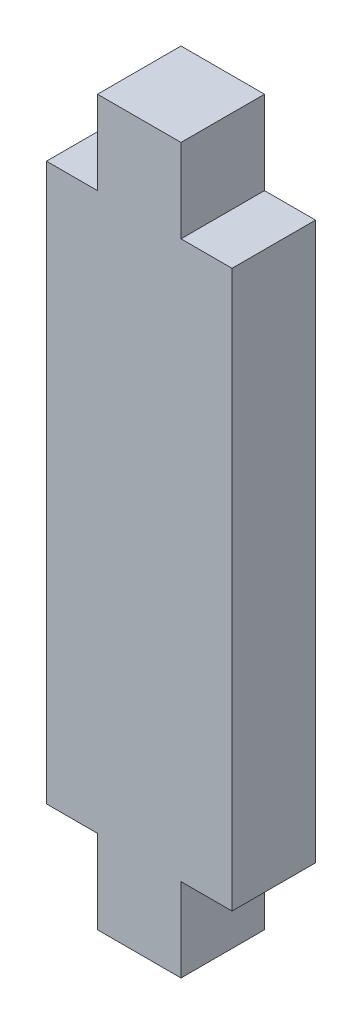
SolidWorks part; units mm, degrees
ref_plane "Front Plane" through (0, 0, 0) normal (0, 0, 1) x (1, 0, 0)
ref_plane "Top Plane" through (0, 0, 0) normal (0, 1, 0) x (1, 0, 0)
ref_plane "Right Plane" through (0, 0, 0) normal (1, 0, 0) x (0, 0, -1)
sketch "Sketch2" plane through (0, 0, 0) normal (0, 0, 1) x (1, 0, 0)
  line L1 (-5, 15) -> (5, 15)
  line L2 (-5, 15) -> (-5, 0)
  line L3 (-5, 0) -> (5, 0)
  line L4 (5, 15) -> (5, 0)
  line L5 (-2.25, 19.5) -> (2.25, 19.5)
  line L6 (-2.25, 19.5) -> (-2.25, 15)
  line L7 (-2.25, 15) -> (2.25, 15)
  line L8 (2.25, 19.5) -> (2.25, 15)
  dimension "D1" = 10
  dimension "D2" = 15
  dimension "D3" = 4.5
  dimension "D4" = 4.5
  dimension "D5" = 5
  dimension "D6" = 15
  dimension "D7" = 2.25
extrude "Boss-Extrude1" add sketch "Sketch2" against normal mid plane 4.5 contours L8 L5 L6 L1 | L4 L1 L2 L3
mirror "Mirror1" about plane through (0, 0, 0) normal (0, 1, 0) of bodies 101
equation "\"D5@Sketch2\"=(\"D1@Sketch2\")/2"
equation "\"D6@Sketch2\"=(\"D2@Sketch2\")"
equation "\"D7@Sketch2\"=(\"D3@Sketch2\")/2"
